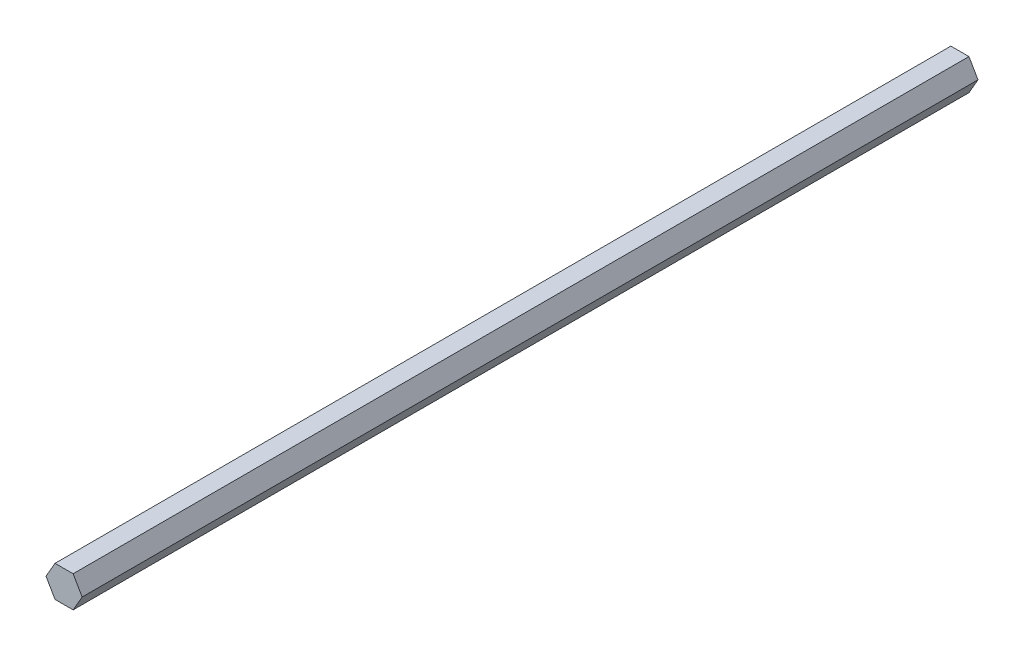
SolidWorks part; units mm, degrees
ref_plane "Front Plane" through (0, 0, 0) normal (0, 0, 1) x (1, 0, 0)
ref_plane "Top Plane" through (0, 0, 0) normal (0, 1, 0) x (1, 0, 0)
ref_plane "Right Plane" through (0, 0, 0) normal (1, 0, 0) x (0, 0, -1)
sketch "Sketch1" plane through (0, 0, 0) normal (0, 0, 1) x (1, 0, 0)
  line L1 (-3.665, 6.348) -> (-7.33, 0)
  line L2 (-7.33, 0) -> (-3.665, -6.348)
  line L3 (-3.665, -6.348) -> (3.665, -6.348)
  line L4 (3.665, -6.348) -> (7.33, 0)
  line L5 (7.33, 0) -> (3.665, 6.348)
  line L6 (3.665, 6.348) -> (-3.665, 6.348)
  circle A0 centre (0, 0) radius 6.348 construction
  point P1 (0, 6.348)
  dimension "7.33" = 7.33
extrude "Boss-Extrude1" add sketch "Sketch1" along normal blind 363.18
